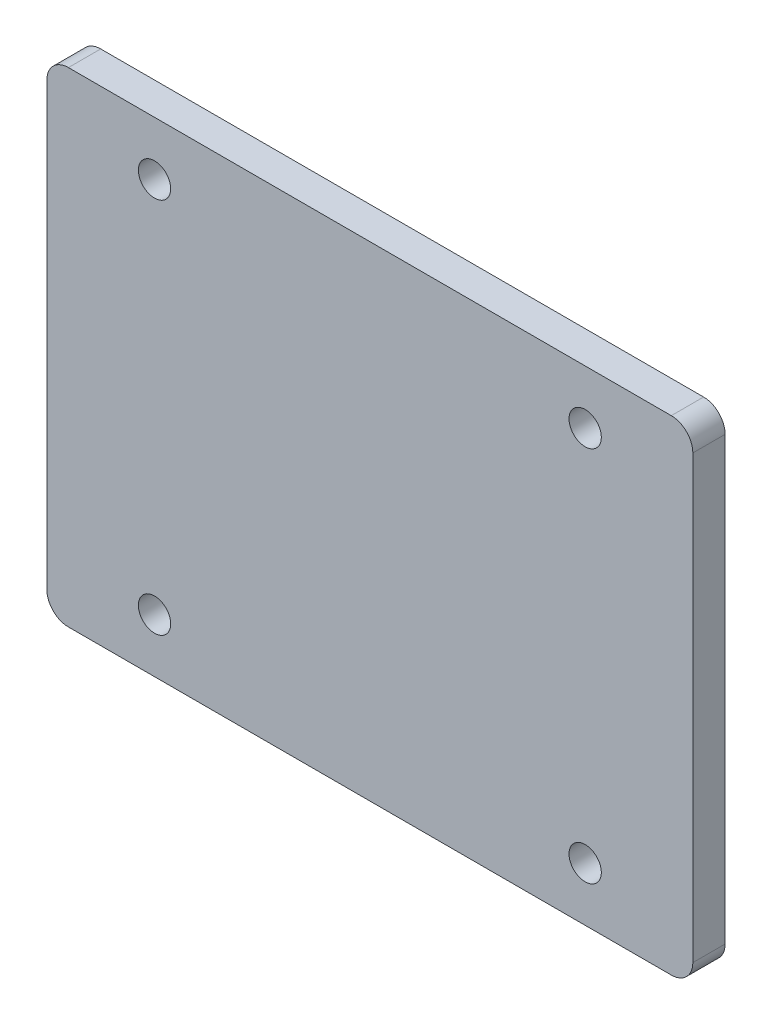
SolidWorks part; units mm, degrees
material "ｱｸﾘﾙ (中-上級の耐衝撃性)"
ref_plane "正面" through (0, 0, 0) normal (0, 0, 1) x (1, 0, 0)
ref_plane "平面" through (0, 0, 0) normal (0, 1, 0) x (1, 0, 0)
ref_plane "右側面" through (0, 0, 0) normal (1, 0, 0) x (0, 0, -1)
sketch "ｽｹｯﾁ2" plane through (0, 0, 0) normal (0, 0, 1) x (1, 0, 0)
  line L1 (0, 0) -> (60, 0)
  line L2 (0, 0) -> (0, 45)
  line L3 (0, 45) -> (60, 45)
  line L4 (60, 0) -> (60, 45)
extrude "ﾎﾞｽ - 押し出し1" add sketch "ｽｹｯﾁ2" along normal blind 3
fillet "ﾌｨﾚｯﾄ3" radius 2 4 edges at (60, 0, 1.5) (0, 0, 1.5) (0, 45, 1.5) (60, 45, 1.5)
sketch "ｽｹｯﾁ4" plane through (0, 0, 3) normal (0, 0, 1) x (1, 0, 0)
  line L0 (-983.9414, 40) -> (49016.0586, 40) construction
  line L1 (58, 45) -> (2, 45) construction
  line L2 (-975.3482, 5) -> (49024.6518, 5) construction
  line L3 (10, -979.5131) -> (10, 49020.4869) construction
  line L4 (50, -979.453) -> (50, 49020.547) construction
  line L5 (2, 0) -> (58, 0) construction
  line L6 (0, 43) -> (0, 2) construction
  line L7 (60, 2) -> (60, 43) construction
  circle A0 centre (10, 40) radius 1.5
  circle A1 centre (50, 40) radius 1.5
  circle A2 centre (10, 5) radius 1.5
  circle A3 centre (50, 5) radius 1.5
  dimension "D1" = 5
  dimension "D2" = 5
  dimension "D3" = 10
  dimension "D4" = 10
extrude "ｶｯﾄ - 押し出し1" cut sketch "ｽｹｯﾁ4" against normal through all
